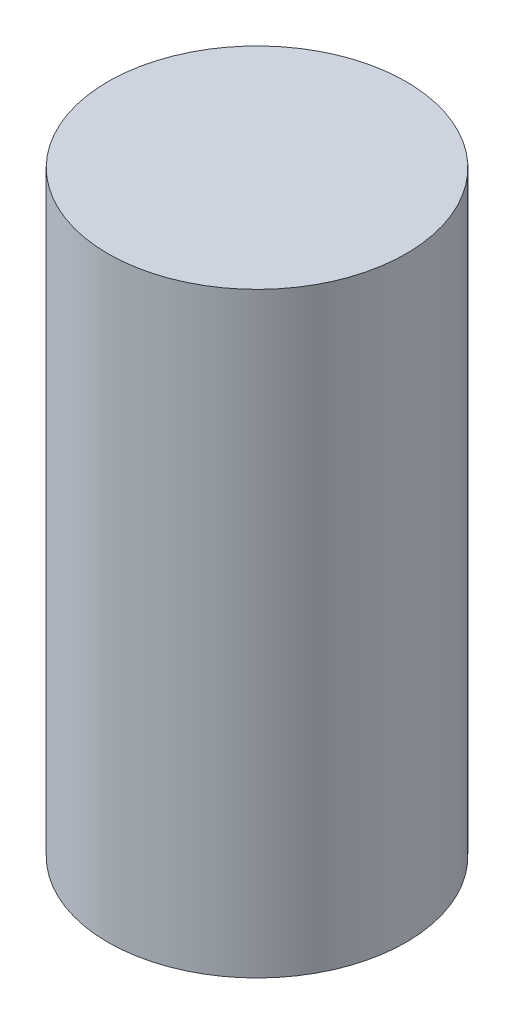
SolidWorks part; units mm, degrees
ref_plane "Front Plane" through (0, 0, 0) normal (0, 0, 1) x (1, 0, 0)
ref_plane "Top Plane" through (0, 0, 0) normal (0, 1, 0) x (1, 0, 0)
ref_plane "Right Plane" through (0, 0, 0) normal (1, 0, 0) x (0, 0, -1)
sketch "Sketch1" plane through (0, 0, 0) normal (0, 1, 0) x (1, 0, 0)
  circle A0 centre (0, 0) radius 50.8
  dimension "D1" = 101.6
extrude "Boss-Extrude1" add sketch "Sketch1" along normal blind 203.2
sketch "Sketch2" plane through (0, 203.2, 0) normal (0, 1, 0) x (1, 0, 0)
  circle A0 centre (0, 0) radius 18.0411
